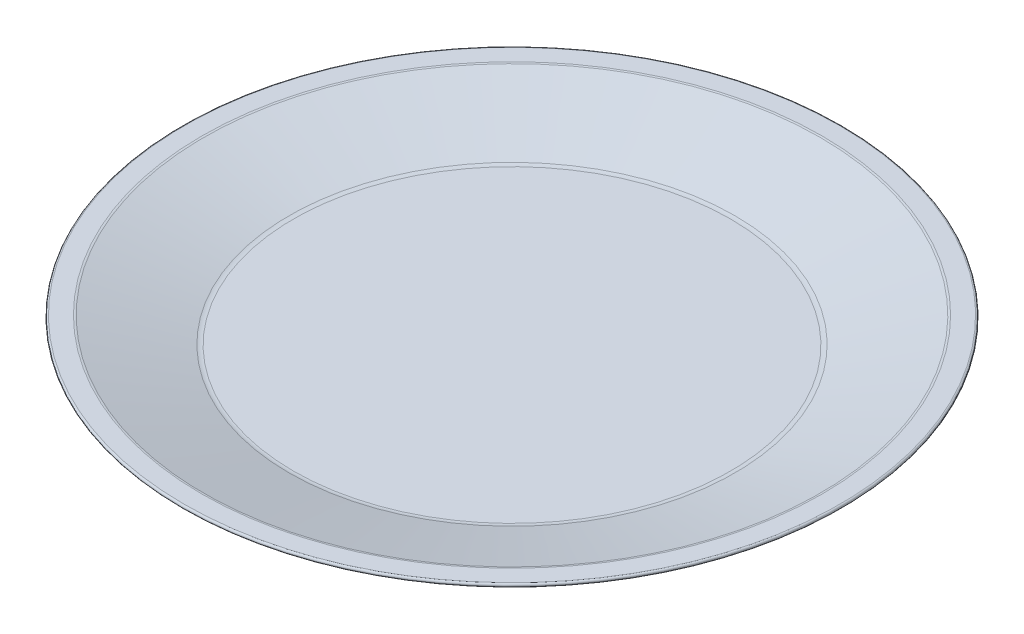
SolidWorks part; units mm, degrees
material "Ceramic Porcelain"
ref_plane "Front Plane" through (0, 0, 0) normal (0, 0, 1) x (1, 0, 0)
ref_plane "Top Plane" through (0, 0, 0) normal (0, 1, 0) x (1, 0, 0)
ref_plane "Right Plane" through (0, 0, 0) normal (1, 0, 0) x (0, 0, -1)
sketch "ProfileS" plane through (0, 0, 0) normal (0, 0, 1) x (1, 0, 0)
  line L0 (0, 0) -> (62.9712, 0)
  line L1 (64.9468, 0.2846) -> (94.6411, 9.0203)
  line L2 (0, 0) -> (0, 10) construction
  line L3 (0, 10) -> (97.9712, 10) construction
  line L4 (0, 2.5) -> (62.9712, 2.5)
  line L5 (64.2412, 2.6829) -> (88.8368, 9.9187)
  line L6 (0, 2.5) -> (0, 0)
  line L7 (94.5, 10) -> (89.4012, 10)
  line L8 (64.9468, 0.2846) -> (97.9712, 10) construction
  line L9 (64.2412, 2.6829) -> (97.2656, 12.3984) construction
  line L10 (97.9712, 10) -> (97.9712, 0) construction
  line L11 (97.9712, 0) -> (0, 0) construction
  line L12 (94.6411, 9.0203) -> (97.9712, 10) construction
  line L13 (95, 10) -> (95, 0) construction
  arc A0 (64.9468, 0.2846) -> (62.9712, 0) centre (62.9712, 7) cw
  arc A1 (64.2412, 2.6829) -> (62.9712, 2.5) centre (62.9712, 7) cw
  arc A2 (94.6411, 9.0203) -> (94.5, 10) centre (94.5, 9.5) ccw
  arc A3 (89.4012, 10) -> (88.8368, 9.9187) centre (89.4012, 8) ccw
  point P18 (89.1132, 10)
  dimension "SWStartRadius" = 7
  dimension "D1" = 0.5
  dimension "D2" = 2
  dimension "Height" = 10
  dimension "SlantedWallWidth" = 35
  dimension "D3" = 95
  dimension "Thickness" = 2.5
revolve "Profile" add sketch "ProfileS" angle 360 about L2
